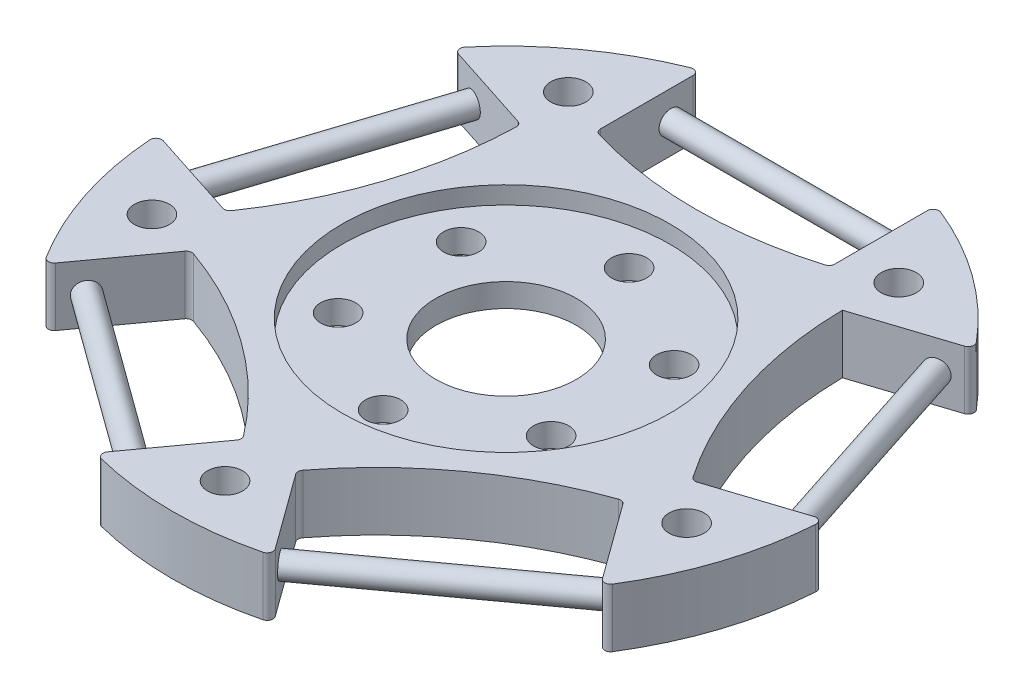
SolidWorks part; units mm, degrees
other "Camera1"
ref_plane "Front Plane" through (0, 0, 0) normal (0, 0, 1) x (1, 0, 0)
ref_plane "Top Plane" through (0, 0, 0) normal (0, 1, 0) x (1, 0, 0)
ref_plane "Right Plane" through (0, 0, 0) normal (1, 0, 0) x (0, 0, -1)
sketch "Sketch1" plane through (0, 0, 0) normal (0, 1, 0) x (1, 0, 0)
  line L0 (0, 0) -> (0, 50000) construction
  line L1 (0, 0) -> (-50000, 0) construction
  circle A0 centre (0, 0) radius 28.5
  dimension "D1" = 57
extrude "Boss-Extrude1" add sketch "Sketch1" along normal blind 5
sketch "Sketch2" plane through (0, 5, 0) normal (0, 1, 0) x (1, 0, 0)
  line L0 (0, 0) -> (13.4182, 0) construction
  line L1 (0, 0) -> (0, 50000) construction
  line L2 (10, 26.688) -> (10, 17.688)
  line L3 (-10, 26.688) -> (-10, 17.688)
  circle A0 centre (0, 0) radius 28.5 construction
  arc A1 (-10, 17.688) -> (10, 17.688) centre (0, 50.0973) ccw
  arc A2 (-10, 26.688) -> (10, 26.688) centre (0, 0) cw
  dimension "D1" = 9
  dimension "D2" = 10
extrude "Cut-Extrude1" cut sketch "Sketch2" against normal through all
pattern_circular "CirPattern1" count 5 over 360 about axis through (0, 0, 0) along (0, 1, 0) of "Cut-Extrude1"
sketch "Sketch3" plane through (0, 5, 0) normal (0, 1, 0) x (1, 0, 0)
  circle A0 centre (0, 0) radius 14
  dimension "D1" = 28
extrude "Cut-Extrude2" cut sketch "Sketch3" against normal blind 1.5
ref_plane "Plane1" through (0, 2.5, 0) normal (0, 1, 0) x (1, 0, 0)
mirror "Mirror1" about plane through (0, 2.5, 0) normal (0, 1, 0) of "Cut-Extrude2"
sketch "Sketch4" plane through (0, 3.5, 0) normal (0, 1, 0) x (1, 0, 0)
  circle A0 centre (0, 10.5) radius 1.5
  circle A1 centre (0, 0) radius 10.5 construction
  circle A2 centre (9.0933, 5.25) radius 1.5
  circle A3 centre (9.0933, -5.25) radius 1.5
  circle A4 centre (0, -10.5) radius 1.5
  circle A5 centre (-9.0933, -5.25) radius 1.5
  circle A6 centre (-9.0933, 5.25) radius 1.5
  circle A7 centre (0, 0) radius 6
  point P18 (0, 0)
  dimension "D2" = 3
  dimension "D4" = 12
  dimension "D1" = 10.5
  dimension "D3" = 6
extrude "Cut-Extrude3" cut sketch "Sketch4" against normal through all
sketch "Sketch5" plane through (0, 5, 0) normal (0, 1, 0) x (1, 0, 0)
  line L0 (0, 0) -> (0, -50000) construction
  circle A0 centre (0, -24) radius 1.5
  dimension "D1" = 24
extrude "Cut-Extrude4" cut sketch "Sketch5" against normal through all
pattern_circular "CirPattern2" count 5 over 360 about axis through (0, 0, 0) along (0, 1, 0) of "Cut-Extrude4"
fillet "Fillet1" radius 0.5 19 edges at (10, 2.5, -17.688) (-10, 2.5, -17.688) (-13.7321, 2.5, -14.9765) (-19.9125, 2.5, 4.0447) (-18.4869, 2.5, 8.4321) (-2.3066, 2.5, 20.1878) (19.9125, 2.5, 4.0447) (18.4869, 2.5, 8.4321) (2.3066, 2.5, 20.1878) (10, 2.5, -26.688) (22.2916, 2.5, -17.7576) (28.472, 2.5, 1.2635) (23.777, 2.5, 15.7132) (7.5967, 2.5, 27.4689) (-7.5967, 2.5, 27.4689) (-23.777, 2.5, 15.7132) (-28.472, 2.5, 1.2635) (-22.2916, 2.5, -17.7576) (-10, 2.5, -26.688)
sketch "Sketch7" plane through (-8.0902, 0, -5.8779) normal (0.809, 0, 0.5878) x (0.5878, 0, -0.809)
  line L1 (-33.8543, 2.5) -> (-18.0591, 2.5) construction
  line L3 (-18.0591, 0) -> (-18.0591, 5) construction
  line L5 (-22.0079, 10) -> (-22.0079, 0) construction
  line L7 (-18.0591, 0) -> (-25.9567, 0) construction
  circle A0 centre (-24.0591, 2.5) radius 1
  point P0 (-25.9567, 2.5)
  point P1 (-22.0079, 5)
  dimension "D1" = 2
  dimension "D2" = 6
extrude "Boss-Extrude2" add sketch "Sketch7" along normal up to next (20 mm away)
pattern_circular "CirPattern3" count 5 over 360 about axis through (0, 3.5, 0) along (0, 1, 0) of "Boss-Extrude2"
scale "ｽｹｰﾙ1" scale about centroid uniform scaling yes scale factor 0.894737
